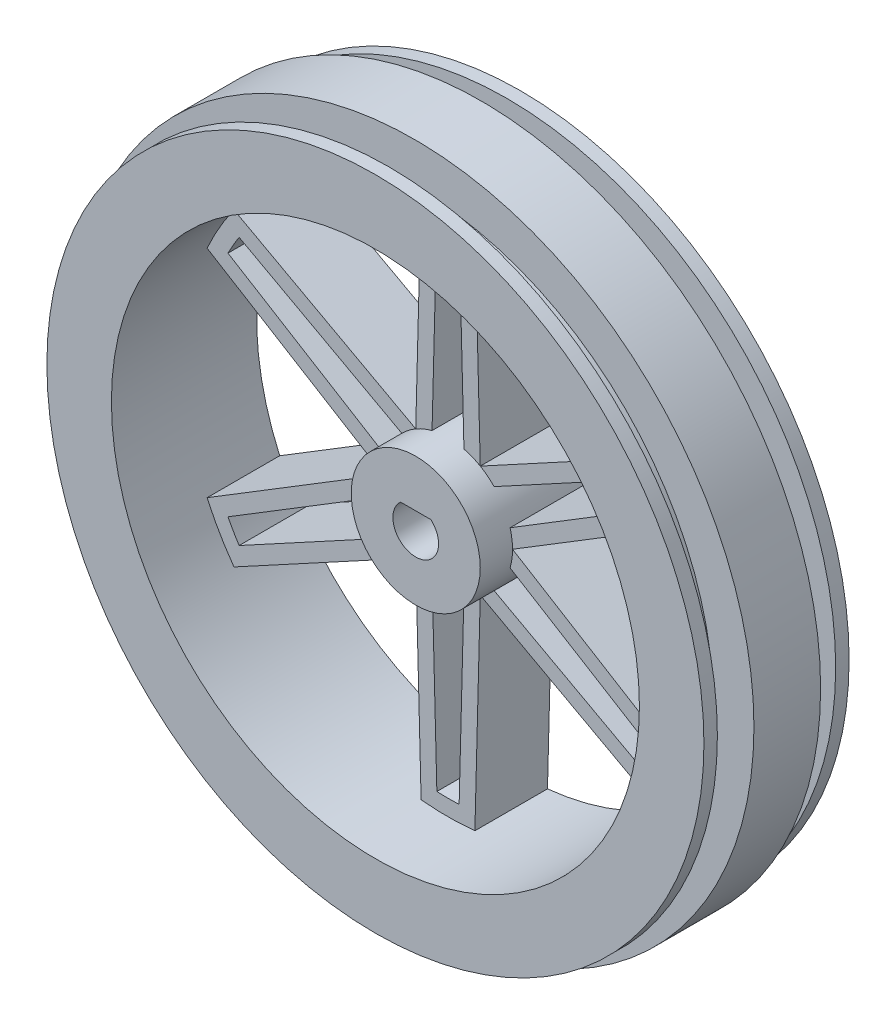
SolidWorks part; units mm, degrees
ref_plane "Front Plane" through (0, 0, 0) normal (0, 0, 1) x (1, 0, 0)
ref_plane "Top Plane" through (0, 0, 0) normal (0, 1, 0) x (1, 0, 0)
ref_plane "Right Plane" through (0, 0, 0) normal (1, 0, 0) x (0, 0, -1)
sketch "Sketch1" plane through (0, 0, 0) normal (0, 1, 0) x (1, 0, 0)
  line L0 (30.55, 6.75) -> (24.55, 6.75)
  line L2 (24.55, 6.75) -> (24.55, -6.75)
  line L3 (30.55, 6.75) -> (30.55, 5.5)
  line L4 (30.55, 5.5) -> (27.75, 5.5)
  line L5 (27.75, 5.5) -> (27.75, 3.1)
  line L6 (27.75, 3.1) -> (31.55, 3.1)
  line L7 (31.55, 3.1) -> (31.55, -3.1)
  line L8 (0, 0) -> (0, 6.75) construction
  line L9 (24.55, 0) -> (31.55, 0) construction
  line L10 (27.75, -3.1) -> (31.55, -3.1)
  line L11 (27.75, -5.5) -> (27.75, -3.1)
  line L12 (30.55, -5.5) -> (27.75, -5.5)
  line L13 (30.55, -6.75) -> (30.55, -5.5)
  line L15 (30.55, -6.75) -> (24.55, -6.75)
  dimension "D1" = 13.5
  dimension "D2" = 2.4
  dimension "D3" = 6.2
  dimension "D4" = 6
  dimension "D5" = 61.1
  dimension "D6" = 2.8
  dimension "D7" = 1
revolve "RIM" add sketch "Sketch1" angle 360 about L8
sketch "Sketch2" plane through (0, 0, 0) normal (0, 0, 1) x (1, 0, 0)
  line L0 (-1.4056, 1.5938) -> (1.4056, 1.5938)
  circle A0 centre (0, 0) radius 6
  arc A1 (-1.4056, 1.5938) -> (1.4056, 1.5938) centre (0, 0) ccw
  point P6 (0, -2.125)
  dimension "SHAFT_DIAM" = 4.25
  dimension "D1" = 12
  dimension "D2" = 3.7188
extrude "HUB" add sketch "Sketch2" against normal up to surface (6.75 mm away) and the other way blind 3 separate body up to face at (24.55, 0, -6.75)
sketch "Sketch3" plane through (0, 0, 0) normal (0, 0, 1) x (1, 0, 0)
  line L0 (-3, 5.1962) -> (-2.5, 24.4224)
  line L1 (3, 5.1962) -> (2.5, 24.4224)
  line L2 (0, 0) -> (0, 40.1741) construction
  line L9 (-1.4834, 5.8137) -> (-1.0358, 23.0267)
  line L10 (1.0358, 23.0267) -> (1.4834, 5.8137)
  circle A0 centre (0, 0) radius 6 construction
  circle A1 centre (0, 0) radius 24.55 construction
  arc A3 (2.5, 24.4224) -> (-2.5, 24.4224) centre (0, 0) ccw
  arc A8 (-1.0358, 23.0267) -> (1.0358, 23.0267) centre (0, 0) cw
  arc A11 (3, 5.1962) -> (1.4834, 5.8137) centre (0, 0) ccw
  arc A12 (-1.4834, 5.8137) -> (-3, 5.1962) centre (0, 0) ccw
  dimension "D4" = 1.5
  dimension "D1" = 5
  dimension "D2" = 6
  dimension "D3" = 1.5
extrude "SPOKE" add sketch "Sketch3" against normal up to surface (6.75 mm away) up to face at (24.55, 0, -6.75)
pattern_circular "CirPattern2" count 6 over 360 about axis through (0, 0, 0) along (0, 0, 1) of "SPOKE"
equation "\"D2@Sketch2\"=7/8*\"SHAFT_DIAM@Sketch2\""
